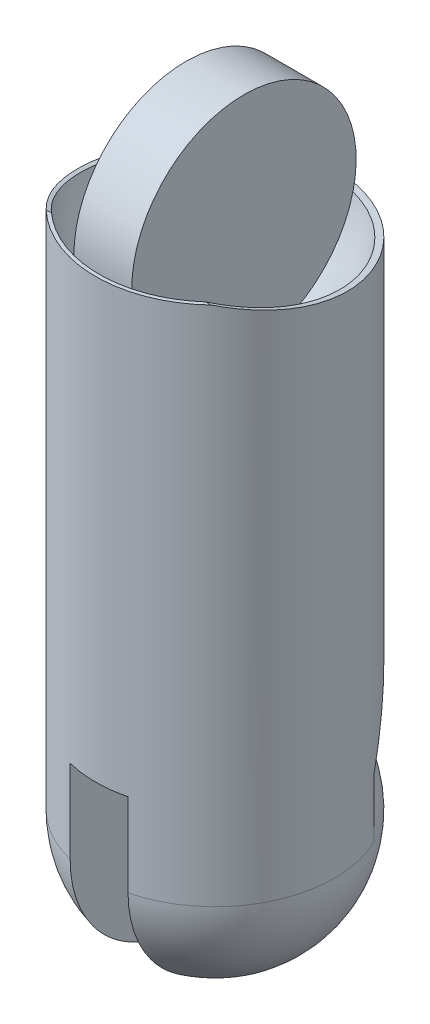
SolidWorks part; units mm, degrees
ref_plane "Alzado" through (0, 0, 0) normal (0, 0, 1) x (1, 0, 0)
ref_plane "Planta" through (0, 0, 0) normal (0, 1, 0) x (1, 0, 0)
ref_plane "Vista lateral" through (0, 0, 0) normal (1, 0, 0) x (0, 0, -1)
sketch "Croquis1" plane through (0, 0, 0) normal (0, 1, 0) x (1, 0, 0)
  circle A0 centre (0, 0) radius 8.25
  dimension "D1" = 16.5
extrude "Saliente-Extruir1" add sketch "Croquis1" along normal blind 36
sketch "Croquis3" plane through (0, 0, 0) normal (1, 0, 0) x (0, 0, -1)
  line L0 (8.25, 0) -> (8.25, 14)
  line L2 (8.25, 0) -> (3.5, 0)
  line L4 (3.5, 4) -> (8.25, 14)
  line L6 (-8.25, 0) -> (8.25, 0) construction
  line L7 (3.5, 0) -> (3.5, 4)
  dimension "D1" = 14
extrude "Cortar-Extruir5" cut sketch "Croquis3" against normal mid plane 36
sketch "Croquis18" plane through (0, 0, 0) normal (1, 0, 0) x (0, 0, -1)
  line L0 (0, 8.25) -> (0, -8.25)
  arc A0 (0, -8.25) -> (0, 8.25) centre (0, 0) ccw
  dimension "D1" = 16.5
revolve "Revolución1" add sketch "Croquis18" angle 360 about L0
sketch "Croquis20" plane through (0, 36, 0) normal (0, 1, 0) x (1, 0, 0)
  line L0 (-8, 0) -> (8, 0)
  arc A0 (8, 0) -> (-8, 0) centre (0, 0) ccw
  dimension "D1" = 16
revolve "Cortar-Revolución1" cut sketch "Croquis20" angle 360 about L0
sketch "Croquis23" plane through (0, 0, 0) normal (1, 0, 0) x (0, 0, -1)
  line L0 (8.25, 36) -> (-8.25, 36) construction
  circle A0 centre (0, 36) radius 7.75
  dimension "D1" = 15.5
sketch "Croquis24" plane through (0, 0, 0) normal (1, 0, 0) x (0, 0, -1)
  line L0 (8.25, 36) -> (-8.25, 36) construction
  line L1 (8.25, 14) -> (8.25, 36) construction
  line L2 (-5.9734, 36) -> (8.25, 36)
  line L3 (8.25, 36) -> (8.25, 34.163)
  spline S0 degree 3 poles (-5.9734, 36) (-1.3781, 34.6045) (3.2819, 34.275) (8.25, 34.163) knots 0 0 0 0 1 1 1 1
extrude "Cortar-Extruir7" cut sketch "Croquis24" against normal mid plane 30
extrude "Saliente-Extruir4" add sketch "Croquis23" along normal mid plane 4 contours A0
sketch "Croquis25" plane through (0, 0, 0) normal (0, 0, 1) x (1, 0, 0)
  line L1 (-2, 5.75) -> (2, 5.75)
  line L2 (2, 5.75) -> (2, -8.25)
  line L3 (2, -8.25) -> (-2, -8.25)
  line L4 (-2, -8.25) -> (-2, 5.75)
  dimension "D2" = 4
extrude "Cortar-Extruir8" cut sketch "Croquis25" against normal mid plane 30
